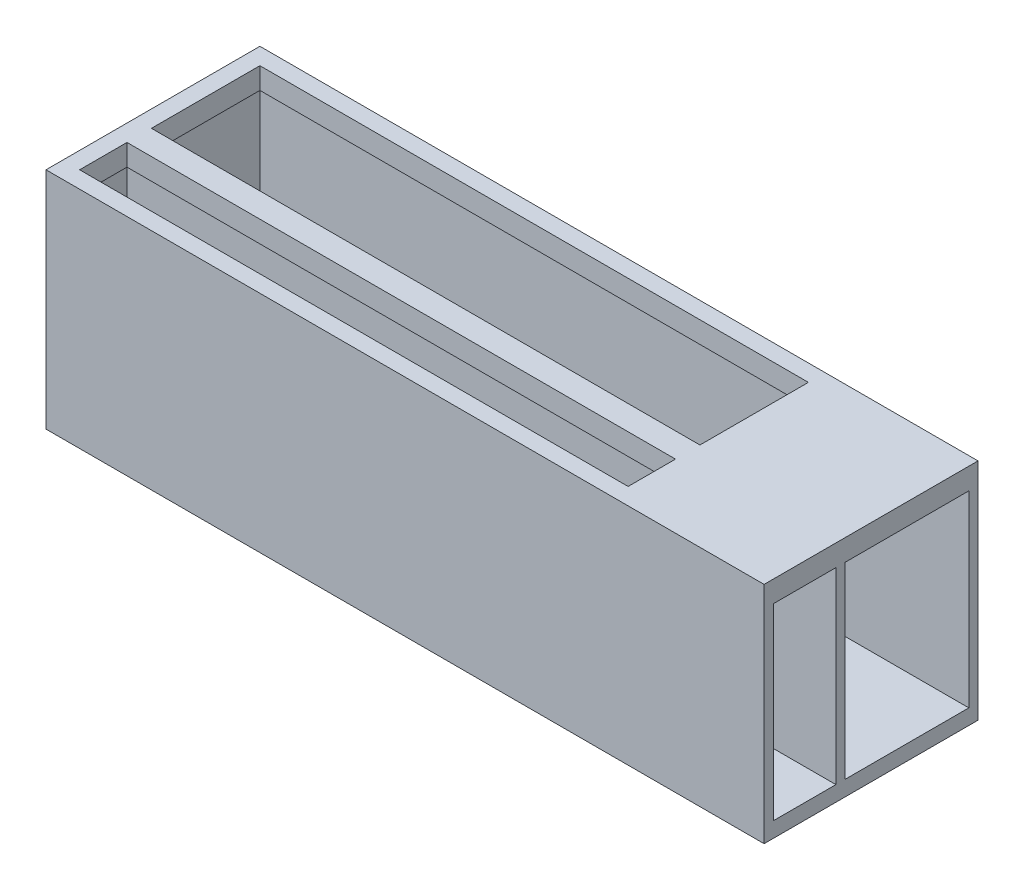
SolidWorks part; units mm, degrees
ref_plane "Front Plane" through (0, 0, 0) normal (0, 0, 1) x (1, 0, 0)
ref_plane "Top Plane" through (0, 0, 0) normal (0, 1, 0) x (1, 0, 0)
ref_plane "Right Plane" through (0, 0, 0) normal (1, 0, 0) x (0, 0, -1)
sketch "Sketch1" plane through (0, 0, 0) normal (0, 1, 0) x (1, 0, 0)
  line L1 (-59.69, 17.78) -> (59.69, 17.78)
  line L2 (-59.69, 17.78) -> (-59.69, -17.78)
  line L3 (-59.69, -17.78) -> (59.69, -17.78)
  line L4 (59.69, 17.78) -> (59.69, -17.78)
  point P4 (0, 17.78)
  point P6 (0, -17.78)
  point P7 (-59.69, 0)
  point P8 (59.69, 0)
  dimension "D1" = 35.56
  dimension "D2" = 119.38
extrude "Boss-Extrude1" add sketch "Sketch1" along normal blind 37.338
sketch "Sketch2" plane through (59.69, 0, 0) normal (1, 0, 0) x (0, 0, -1)
  line L0 (-17.78, 37.338) -> (-17.78, 0) construction
  line L1 (-16.256, 33.782) -> (-5.842, 33.782)
  line L2 (-16.256, 33.782) -> (-16.256, 2.54)
  line L3 (-16.256, 2.54) -> (-5.842, 2.54)
  line L4 (-5.842, 33.782) -> (-5.842, 2.54)
  line L5 (-4.318, 33.782) -> (16.256, 33.782)
  line L6 (-4.318, 33.782) -> (-4.318, 2.54)
  line L7 (-4.318, 2.54) -> (16.256, 2.54)
  line L8 (16.256, 33.782) -> (16.256, 2.54)
  line L9 (17.78, 37.338) -> (17.78, 0) construction
  line L10 (-17.78, 0) -> (17.78, 0) construction
  dimension "D1" = 1.524
  dimension "D2" = 10.414
  dimension "D3" = 20.574
  dimension "D4" = 1.524
  dimension "D5" = 31.242
  dimension "D6" = 2.54
extrude "Cut-Extrude1" cut sketch "Sketch2" against normal offset from surface (117.856 mm away) 1.524 up to face at (-59.69, 18.669, 0)
sketch "Sketch3" plane through (0, 37.338, 0) normal (0, 1, 0) x (1, 0, 0)
  line L0 (-58.166, -16.256) -> (59.69, -16.256) construction
  line L1 (-56.896, 14.986) -> (34.29, 14.986)
  line L2 (-56.896, 14.986) -> (-56.896, -3.048)
  line L3 (-56.896, -3.048) -> (34.29, -3.048)
  line L4 (34.29, 14.986) -> (34.29, -3.048)
  line L9 (-56.896, -7.112) -> (34.29, -7.112)
  line L10 (-56.896, -7.112) -> (-56.896, -14.986)
  line L11 (-56.896, -14.986) -> (34.29, -14.986)
  line L12 (34.29, -7.112) -> (34.29, -14.986)
  line L13 (59.69, -17.78) -> (59.69, 17.78) construction
  line L15 (-58.166, -16.256) -> (59.69, -16.256)
  line L16 (-58.166, -4.318) -> (59.69, -4.318) construction
  line L17 (-58.166, -5.842) -> (59.69, -5.842) construction
  line L18 (-58.166, -4.318) -> (59.69, -4.318)
  line L19 (-58.166, -5.842) -> (59.69, -5.842)
  line L20 (-58.166, 16.256) -> (59.69, 16.256) construction
  line L21 (-58.166, 16.256) -> (59.69, 16.256)
  line L22 (-58.166, -16.256) -> (-58.166, -5.842) construction
  line L23 (-58.166, -4.318) -> (-58.166, 16.256) construction
  line L24 (-58.166, -16.256) -> (-58.166, -5.842)
  line L25 (-58.166, -4.318) -> (-58.166, 16.256)
  dimension "D1" = 1.27
  dimension "D2" = 1.27
  dimension "D3" = 1.27
  dimension "D4" = 1.27
  dimension "D5" = 1.27
  dimension "D6" = 1.27
  dimension "D7" = 25.4
  dimension "D8" = 25.4
extrude "Cut-Extrude2" cut sketch "Sketch3" against normal up to next contours L4 L1 L2 L3 | L12 L9 L10 L11
ref_plane "Plane1" through (0, 16.51, 0) normal (0, -1, 0) x (-1, 0, 0)
